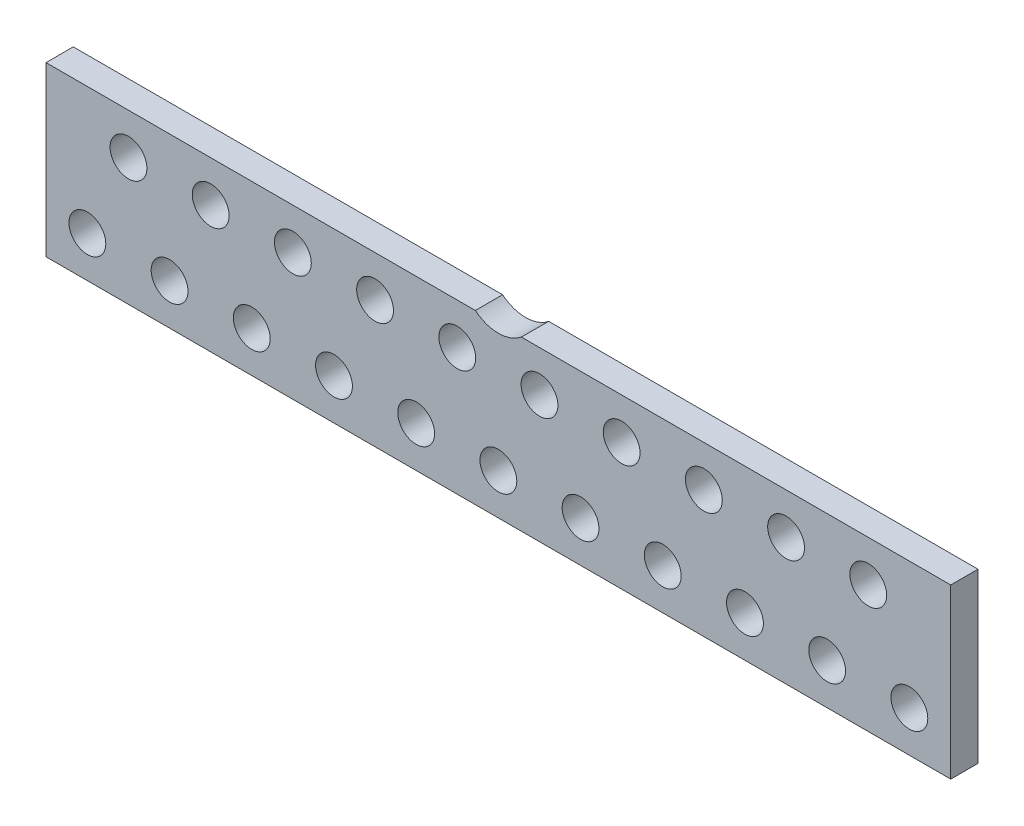
SolidWorks part; units mm, degrees
ref_plane "Front Plane" through (0, 0, 0) normal (0, 0, 1) x (1, 0, 0)
ref_plane "Top Plane" through (0, 0, 0) normal (0, 1, 0) x (1, 0, 0)
ref_plane "Right Plane" through (0, 0, 0) normal (1, 0, 0) x (0, 0, -1)
ref_plane "mating plane between carrier PCBs" through (0, 0, 2.26) normal (0, 0, 1) x (1, 0, 0)
sketch "Sketch1" plane through (0, 0, 2.26) normal (0, 0, 1) x (1, 0, 0)
  line L0 (-1.0084, 3.683) -> (-19.812, 3.683)
  line L1 (-19.812, 3.683) -> (19.812, 3.683) construction
  line L2 (-19.812, 3.683) -> (-19.812, -3.683)
  line L3 (-19.812, -3.683) -> (19.812, -3.683)
  line L4 (19.812, 3.683) -> (19.812, -3.683)
  line L5 (1.0084, 3.683) -> (19.812, 3.683)
  circle A0 centre (0, 4.915) radius 1.588 construction
  arc A1 (-1.0084, 3.683) -> (1.0084, 3.683) centre (0, 4.915) ccw
extrude "Boss-Extrude1" add sketch "Sketch1" against normal blind 1.194 contours L0 L2 L3 L4 L5 A1
sketch "Sketch2" plane through (0, 0, 2.26) normal (0, 0, 1) x (1, 0, 0)
  circle A0 centre (-18, -1.885) radius 0.8065
  circle A1 centre (-16.2, 1.885) radius 0.8065
  circle A2 centre (-14.4, -1.885) radius 0.8065
  circle A3 centre (-10.8, -1.885) radius 0.8065
  circle A4 centre (-7.2, -1.885) radius 0.8065
  circle A5 centre (-3.6, -1.885) radius 0.8065
  circle A6 centre (0, -1.885) radius 0.8065
  circle A7 centre (3.6, -1.885) radius 0.8065
  circle A8 centre (7.2, -1.885) radius 0.8065
  circle A9 centre (10.8, -1.885) radius 0.8065
  circle A10 centre (14.4, -1.885) radius 0.8065
  circle A11 centre (18, -1.885) radius 0.8065
  circle A12 centre (-12.6, 1.885) radius 0.8065
  circle A13 centre (-9, 1.885) radius 0.8065
  circle A14 centre (-5.4, 1.885) radius 0.8065
  circle A15 centre (-1.8, 1.885) radius 0.8065
  circle A16 centre (1.8, 1.885) radius 0.8065
  circle A17 centre (5.4, 1.885) radius 0.8065
  circle A18 centre (9, 1.885) radius 0.8065
  circle A19 centre (12.6, 1.885) radius 0.8065
  circle A20 centre (16.2, 1.885) radius 0.8065
  point P0 (-18, -1.885)
  point P1 (-16.2, 1.885)
  point P3 (-12.6, 1.885)
  point P4 (-14.4, -1.885)
  point P5 (-10.8, -1.885)
  point P6 (-7.2, -1.885)
  point P7 (-3.6, -1.885)
  point P8 (0, -1.885)
  point P9 (3.6, -1.885)
  point P10 (7.2, -1.885)
  point P11 (10.8, -1.885)
  point P12 (14.4, -1.885)
  point P13 (18, -1.885)
  point P14 (-9, 1.885)
  point P15 (-5.4, 1.885)
  point P16 (-1.8, 1.885)
  point P17 (1.8, 1.885)
  point P18 (5.4, 1.885)
  point P19 (9, 1.885)
  point P20 (12.6, 1.885)
  point P21 (16.2, 1.885)
  dimension "D1" = 11
  dimension "D2" = 10
extrude "Cut-Extrude1" cut sketch "Sketch2" against normal through all
